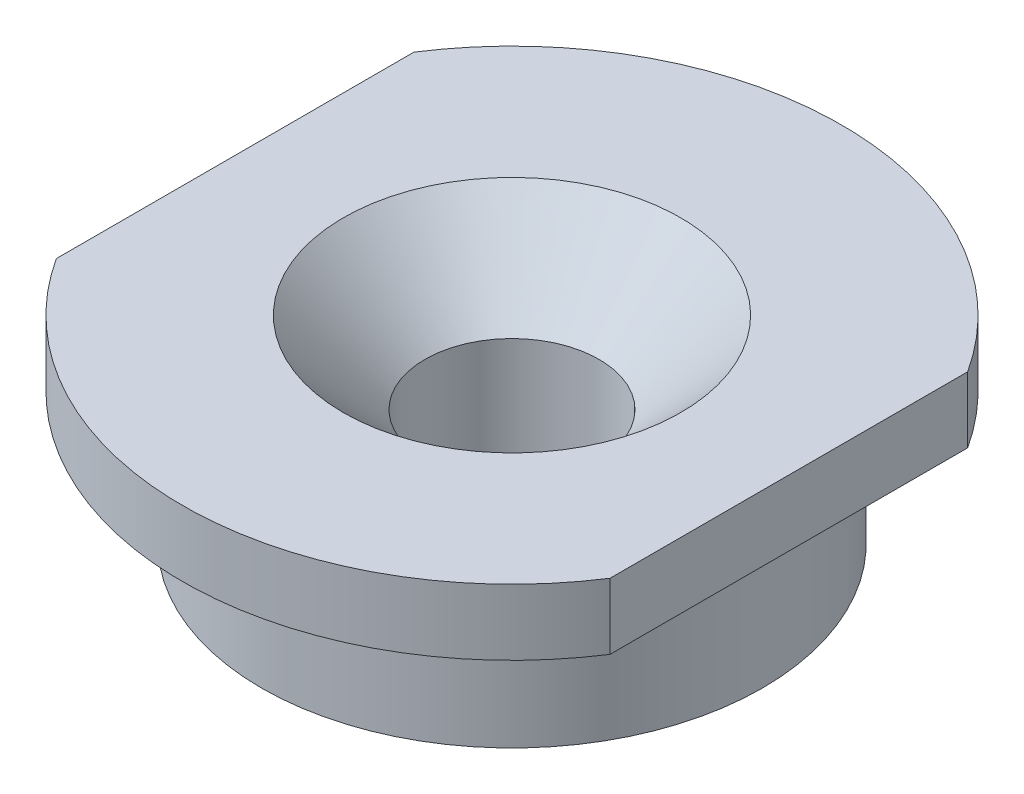
SolidWorks part; units mm, degrees
material "A3钢"
ref_plane "前视基准面" through (0, 0, 0) normal (0, 0, 1) x (1, 0, 0)
ref_plane "上视基准面" through (0, 0, 0) normal (0, 1, 0) x (1, 0, 0)
ref_plane "右视基准面" through (0, 0, 0) normal (1, 0, 0) x (0, 0, -1)
sketch "草图1" plane through (0, 0, 0) normal (0, 0, 1) x (1, 0, 0)
  line L0 (0, 11.114) -> (0, -7.0614) construction
  line L1 (0, 0) -> (9.5, 0)
  line L2 (9.5, 0) -> (9.5, 5)
  line L3 (9.5, 5) -> (12.5, 5)
  line L4 (12.5, 5) -> (12.5, 7.5)
  line L5 (12.5, 7.5) -> (0, 7.5)
  line L6 (0, 0) -> (0, 7.5)
  dimension "D1" = 19
  dimension "D2" = 25
  dimension "D3" = 5
  dimension "D4" = 2.5
revolve "旋转1" add sketch "草图1" angle 360 about L0
hole_wizard "打孔尺寸(%根据)内六角花形半沉头螺钉的类型1" positions "3D草图1" profile "草图2" countersink size "M6" standard "GB" end condition through all
sketch3d "3D草图1"
  line L0 (0, 5, 0) -> (0, 7.5, 0) construction
  point P0 (0, 7.5, 0)
sketch "草图2" plane through (0, 7.5, 0) normal (1, 0, 0) x (0, 0, 1)
  line L0 (0, 0) -> (0, 7.5)
  line L1 (0, 7.5) -> (3.3, 7.5)
  line L2 (3.3, 7.5) -> (3.3, 3.1)
  line L3 (3.3, 3.1) -> (6.4, 0)
  line L5 (6.4, 0) -> (0, 0)
  line L6 (-3.3, 3.1) -> (-6.4, 0) construction
  line L11 (0, -6.35) -> (0, 107.95) construction
  dimension "通孔孔直径" = 6.6
  dimension "通孔孔深度" = 7.5
  dimension "近端锥形沉头孔直径" = 12.8
  dimension "近端锥形沉头孔角度" = 90
sketch "草图3" plane through (0, 0, 0) normal (0, 0, 1) x (1, 0, 0)
  line L0 (-12.5, 5) -> (12.5, 5) construction
  line L1 (-10.5, 5) -> (-12.5, 5)
  line L2 (-10.5, 5) -> (-10.5, 7.5)
  line L3 (-10.5, 7.5) -> (-12.5, 7.5)
  line L4 (-12.5, 5) -> (-12.5, 7.5)
  line L5 (-10.5, 5) -> (-12.5, 7.5) construction
  line L6 (-10.5, 7.5) -> (-12.5, 5) construction
  line L7 (0, 0) -> (0, 25.2879) construction
  line L8 (10.5, 7.5) -> (12.5, 5) construction
  line L9 (10.5, 5) -> (12.5, 7.5) construction
  line L10 (12.5, 5) -> (12.5, 7.5)
  line L11 (10.5, 7.5) -> (12.5, 7.5)
  line L12 (10.5, 5) -> (10.5, 7.5)
  line L13 (10.5, 5) -> (12.5, 5)
  point P0 (-11.5, 6.25)
  point P15 (11.5, 6.25)
  dimension "D1" = 2
extrude "切除-拉伸1" cut sketch "草图3" against normal through all both and the other way through all
